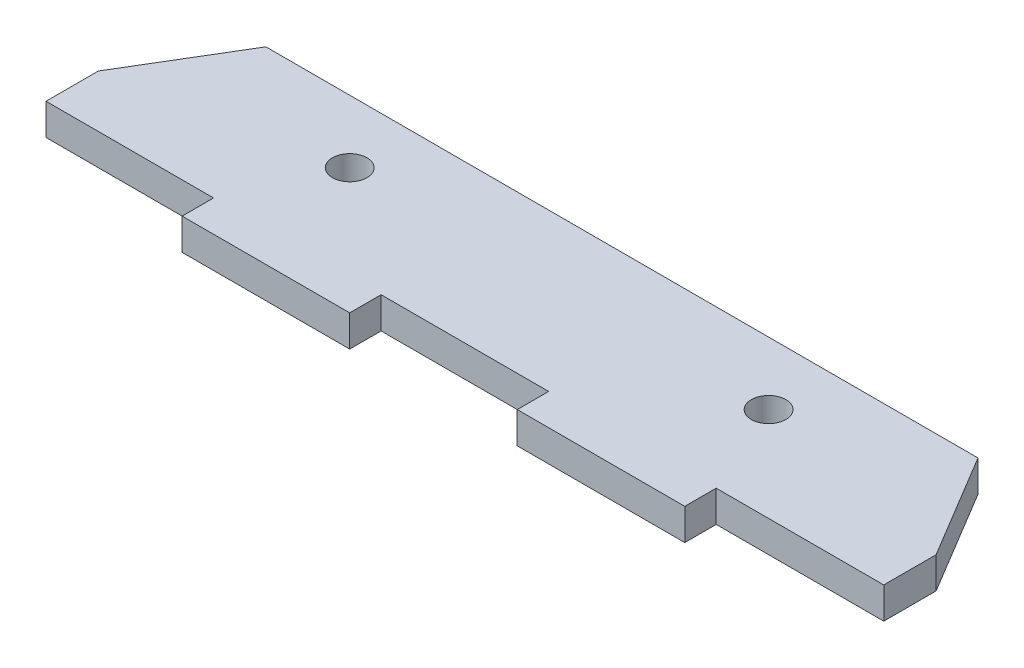
SolidWorks part; units mm, degrees
ref_plane "Ön Düzlem" through (0, 0, 0) normal (0, 0, 1) x (1, 0, 0)
ref_plane "Üst Düzlem" through (0, 0, 0) normal (0, 1, 0) x (1, 0, 0)
ref_plane "Sağ Düzlem" through (0, 0, 0) normal (1, 0, 0) x (0, 0, -1)
sketch "Sketch1" plane through (0, 0, 0) normal (0, 1, 0) x (1, 0, 0)
  line L0 (-40, -1) -> (-34, 9)
  line L1 (-34, 9) -> (34, 9)
  line L2 (-40, -1) -> (-40, -6)
  line L3 (-24, -9) -> (-8, -9)
  line L4 (40, -1) -> (40, -6)
  line L7 (34, 9) -> (40, -1)
  line L9 (-40, -6) -> (-24, -6)
  line L10 (-24, -6) -> (-24, -9)
  line L11 (-8, -9) -> (-8, -6)
  line L12 (-8, -6) -> (8, -6)
  line L13 (8, -6) -> (8, -9)
  line L14 (8, -9) -> (24, -9)
  line L15 (24, -9) -> (24, -6)
  line L16 (24, -6) -> (40, -6)
  circle A0 centre (-20, 3.0031) radius 1.65
  circle A1 centre (20, 3.0031) radius 1.65
  point P0 (0, 0)
  dimension "D1" = 20
extrude "Boss-Extrude1" add sketch "Sketch1" along normal blind 3
